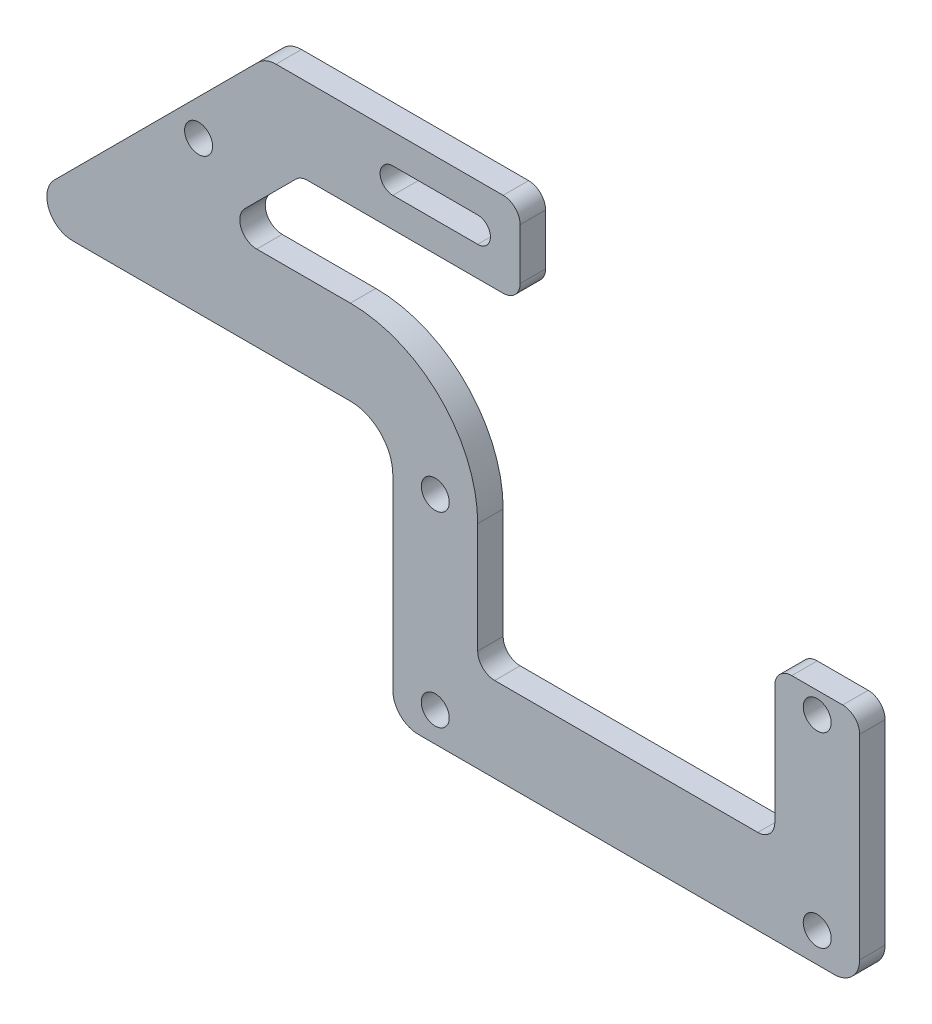
SolidWorks part; units mm, degrees
material "A-玻璃纤维"
ref_plane "前视基准面" through (0, 0, 0) normal (0, 0, 1) x (1, 0, 0)
ref_plane "上视基准面" through (0, 0, 0) normal (0, 1, 0) x (1, 0, 0)
ref_plane "右视基准面" through (0, 0, 0) normal (1, 0, 0) x (0, 0, -1)
sketch "草图1" plane through (0, 0, 0) normal (0, 0, 1) x (1, 0, 0)
  line L0 (0, 0) -> (0, 55.166) construction
  line L1 (22.5, 0) -> (-22.5, 0) construction
  line L2 (-22.5, 0) -> (-22.5, 22) construction
  line L3 (22.5, 0) -> (22.5, 22) construction
  line L4 (27.5, -3.5) -> (-27.5, -3.5)
  line L5 (-27.5, -3.5) -> (-27.5, 26.5)
  line L6 (-27.5, 26.5) -> (27.5, 26.5)
  line L7 (0, 0) -> (0, -3.5) construction
  line L8 (27.5, -3.5) -> (27.5, 26.5)
  circle A0 centre (-22.5, 0) radius 1.65
  circle A1 centre (-22.5, 22) radius 1.65
  circle A2 centre (22.5, 22) radius 1.65
  circle A3 centre (22.5, 0) radius 1.65
  point P16 (0, 26.5)
  dimension "D2" = 3.3
  dimension "D4" = 3.3
  dimension "D1" = 22.5
  dimension "D3" = 22
  dimension "D5" = 3.5
  dimension "D6" = 30
  dimension "D7" = 55
extrude "凸台-拉伸1" add sketch "草图1" along normal blind 3
sketch "草图2" plane through (0, 0, 3) normal (0, 0, 1) x (1, 0, 0)
  line L0 (0, 0) -> (0, 56.5) construction
  line L1 (27.5, 26.5) -> (-27.5, 26.5) construction
  line L2 (27.5, 26.5) -> (27.5, 56.5)
  line L3 (27.5, 56.5) -> (-27.5, 56.5)
  line L4 (-27.5, 56.5) -> (-27.5, 26.5)
  line L5 (-27.5, 26.5) -> (27.5, 26.5)
  dimension "D1" = 30
extrude "凸台-拉伸2" add sketch "草图2" against normal up to surface (3 mm away) up to face at (20.85, 22, 0)
sketch "草图4" plane through (0, 0, 3) normal (0, 0, 1) x (1, 0, 0)
  line L0 (-27.5, 26.5) -> (-72.5, 26.5)
  line L1 (-27.5, 56.5) -> (-27.5, -3.5) construction
  line L4 (-27.5, 56.5) -> (-42.5, 56.5)
  line L5 (-42.5, 56.5) -> (-72.5, 26.5)
  line L6 (-27.5, 56.5) -> (-27.5, 26.5)
  dimension "D1" = 15
  dimension "D2" = 45
  dimension "D3" = 30
extrude "凸台-拉伸3" add sketch "草图4" against normal up to surface (3 mm away) up to face at (20.85, 22, 0)
sketch "草图8" plane through (0, 0, 0) normal (0, 0, -1) x (-1, 0, 0)
  line L0 (52.5, 46.5) -> (50.3787, 44.3787) construction
  line L1 (42.5, 56.5) -> (72.5, 26.5) construction
  line L2 (-27.5, 56.5) -> (42.5, 56.5) construction
  circle A0 centre (50.3787, 44.3787) radius 1.65
  dimension "D2" = 3.3
  dimension "D1" = 10
  dimension "D3" = 3
extrude "切除-拉伸1" cut sketch "草图8" against normal blind 10
fillet "圆角1" radius 5 1 edges at (-27.5, 26.5, 1.5)
fillet "圆角2" radius 3 5 edges at (-27.5, -3.5, 1.5) (27.5, -3.5, 1.5) (27.5, 56.5, 1.5) (-42.5, 56.5, 1.5) (-72.5, 26.5, 1.5)
sketch "草图9" plane through (0, 0, 0) normal (0, 0, -1) x (-1, 0, 0)
  line L0 (22.5, 56.5) -> (22.5, 51.5) construction
  line L2 (17.5, 51.5) -> (27.5, 51.5) construction
  line L3 (17.5, 53) -> (27.5, 53)
  line L4 (17.5, 50) -> (27.5, 50)
  line L5 (-27.5, -0.5) -> (-27.5, 53.5) construction
  line L6 (-24.5, 56.5) -> (41.2574, 56.5) construction
  arc A0 (17.5, 53) -> (17.5, 50) centre (17.5, 51.5) ccw
  arc A1 (27.5, 50) -> (27.5, 53) centre (27.5, 51.5) ccw
  point P6 (22.5, 51.5)
  dimension "D2" = 1.5
  dimension "D1" = 5
  dimension "D3" = 10
  dimension "D4" = 50
  dimension "D5" = 5
extrude "切除-拉伸2" cut sketch "草图9" against normal blind 10
sketch "草图10" plane through (0, 0, 0) normal (0, 0, -1) x (-1, 0, 0)
  line L0 (-15.5, 6.5) -> (15.5, 6.5)
  line L1 (17.5, 8.5) -> (17.5, 21.5)
  line L2 (32.5, 36.5) -> (43.5294, 36.5)
  line L3 (44.9437, 39.9142) -> (38.9437, 45.9142)
  line L4 (37.5294, 46.5) -> (-15.5, 46.5)
  line L5 (-17.5, 44.5) -> (-17.5, 8.5)
  line L6 (-24.5, -3.5) -> (24.5, -3.5)
  line L7 (27.5, -0.5) -> (27.5, 21.5)
  line L8 (32.5, 26.5) -> (65.2574, 26.5)
  line L9 (67.3787, 31.6213) -> (43.3787, 55.6213)
  line L10 (41.2574, 56.5) -> (-24.5, 56.5)
  line L11 (-27.5, 53.5) -> (-27.5, -0.5)
  line L12 (-24.5, -3.5) -> (24.5, -3.5) construction
  line L13 (27.5, -0.5) -> (27.5, 21.5) construction
  line L14 (32.5, 26.5) -> (65.2574, 26.5) construction
  line L15 (67.3787, 31.6213) -> (43.3787, 55.6213) construction
  line L16 (41.2574, 56.5) -> (-24.5, 56.5) construction
  line L17 (-27.5, 53.5) -> (-27.5, -0.5) construction
  line L18 (38.3579, 46.5) -> (-17.5, 46.5) construction
  line L19 (48.3579, 36.5) -> (38.3579, 46.5) construction
  line L20 (32.5, 36.5) -> (48.3579, 36.5) construction
  line L21 (17.5, 6.5) -> (17.5, 21.5) construction
  line L22 (-17.5, 6.5) -> (17.5, 6.5) construction
  line L23 (-17.5, 46.5) -> (-17.5, 6.5) construction
  arc A1 (32.5, 36.5) -> (17.5, 21.5) centre (32.5, 21.5) ccw
  arc A6 (24.5, -3.5) -> (27.5, -0.5) centre (24.5, -0.5) ccw
  arc A7 (32.5, 26.5) -> (27.5, 21.5) centre (32.5, 21.5) ccw
  arc A8 (65.2574, 26.5) -> (67.3787, 31.6213) centre (65.2574, 29.5) ccw
  arc A9 (43.3787, 55.6213) -> (41.2574, 56.5) centre (41.2574, 53.5) ccw
  arc A10 (-24.5, 56.5) -> (-27.5, 53.5) centre (-24.5, 53.5) ccw
  arc A11 (-27.5, -0.5) -> (-24.5, -3.5) centre (-24.5, -0.5) ccw
  arc A12 (24.5, -3.5) -> (27.5, -0.5) centre (24.5, -0.5) ccw construction
  arc A13 (32.5, 26.5) -> (27.5, 21.5) centre (32.5, 21.5) ccw construction
  arc A14 (65.2574, 26.5) -> (67.3787, 31.6213) centre (65.2574, 29.5) ccw construction
  arc A15 (43.3787, 55.6213) -> (41.2574, 56.5) centre (41.2574, 53.5) ccw construction
  arc A16 (-24.5, 56.5) -> (-27.5, 53.5) centre (-24.5, 53.5) ccw construction
  arc A17 (-27.5, -0.5) -> (-24.5, -3.5) centre (-24.5, -0.5) ccw construction
  arc A18 (37.5294, 46.5) -> (38.9437, 45.9142) centre (37.5294, 44.5) cw
  arc A19 (38.3579, 46.5) -> (38.3579, 46.5) centre (38.3579, 46.5) ccw construction
  arc A20 (44.9437, 39.9142) -> (43.5294, 36.5) centre (43.5294, 38.5) cw
  arc A21 (48.3579, 36.5) -> (48.3579, 36.5) centre (48.3579, 36.5) ccw construction
  arc A22 (17.5, 8.5) -> (15.5, 6.5) centre (15.5, 8.5) cw
  arc A23 (17.5, 6.5) -> (17.5, 6.5) centre (17.5, 6.5) ccw construction
  arc A24 (-15.5, 6.5) -> (-17.5, 8.5) centre (-15.5, 8.5) cw
  arc A25 (-17.5, 6.5) -> (-17.5, 6.5) centre (-17.5, 6.5) ccw construction
  arc A26 (-15.5, 46.5) -> (-17.5, 44.5) centre (-15.5, 44.5) ccw
  arc A27 (-17.5, 46.5) -> (-17.5, 46.5) centre (-17.5, 46.5) ccw construction
  dimension "D3" = 2
  dimension "D1" = 0
  dimension "D2" = 10
extrude "切除-拉伸3" cut sketch "草图10" against normal through all
sketch "草图11" plane through (0, 0, 0) normal (0, 0, -1) x (-1, 0, 0)
  line L0 (-27.5, 24.5) -> (12.5, 24.5)
  line L1 (12.5, 24.5) -> (12.5, 56.5)
  line L6 (-24.5, -3.5) -> (24.5, -3.5)
  line L7 (27.5, -0.5) -> (27.5, 21.5)
  line L8 (32.5, 26.5) -> (65.2574, 26.5)
  line L9 (67.3787, 31.6213) -> (43.3787, 55.6213)
  line L10 (41.2574, 56.5) -> (-24.5, 56.5)
  line L11 (-27.5, 53.5) -> (-27.5, -0.5)
  line L16 (12.5, 56.5) -> (-24.5, 56.5)
  line L17 (-27.5, 53.5) -> (-27.5, 24.5)
  arc A6 (24.5, -3.5) -> (27.5, -0.5) centre (24.5, -0.5) ccw
  arc A7 (32.5, 26.5) -> (27.5, 21.5) centre (32.5, 21.5) ccw
  arc A8 (65.2574, 26.5) -> (67.3787, 31.6213) centre (65.2574, 29.5) ccw
  arc A9 (43.3787, 55.6213) -> (41.2574, 56.5) centre (41.2574, 53.5) ccw
  arc A10 (-24.5, 56.5) -> (-27.5, 53.5) centre (-24.5, 53.5) ccw
  arc A11 (-27.5, -0.5) -> (-24.5, -3.5) centre (-24.5, -0.5) ccw
  arc A16 (-24.5, 56.5) -> (-27.5, 53.5) centre (-24.5, 53.5) ccw
  dimension "D2" = 32
  dimension "D3" = 40
  dimension "D1" = 0
extrude "切除-拉伸4" cut sketch "草图11" against normal through all
fillet "圆角3" radius 2 4 edges at (27.5, 24.5, 1.5) (17.5, 24.5, 1.5) (-12.5, 56.5, 1.5) (-12.5, 46.5, 1.5)
